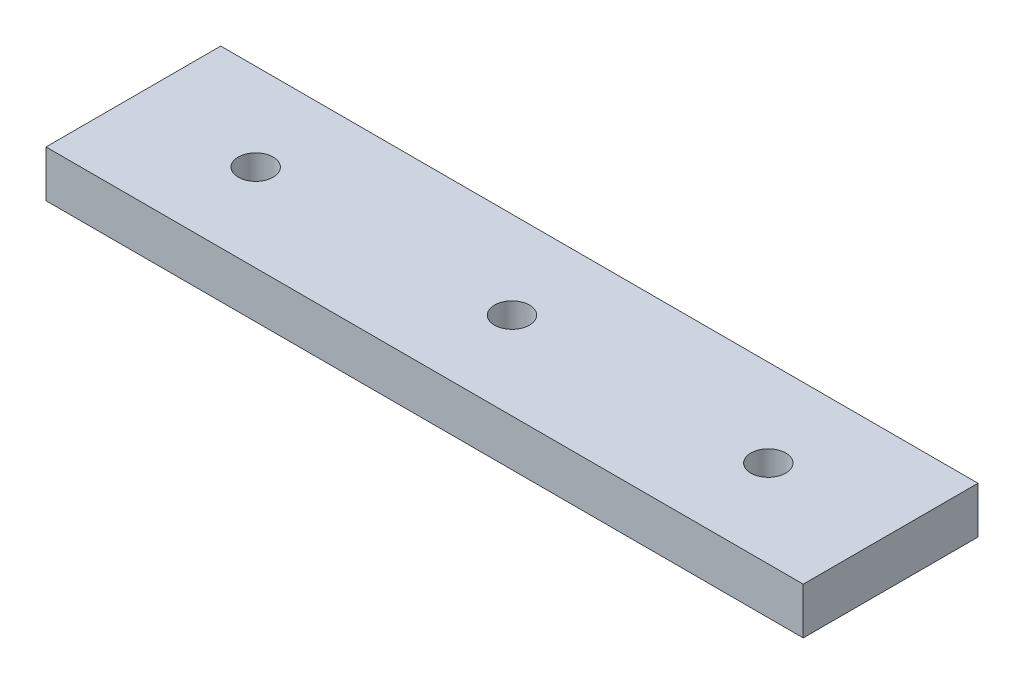
SolidWorks part; units mm, degrees
ref_plane "Alzado" through (0, 0, 0) normal (0, 0, 1) x (1, 0, 0)
ref_plane "Planta" through (0, 0, 0) normal (0, 1, 0) x (1, 0, 0)
ref_plane "Vista lateral" through (0, 0, 0) normal (1, 0, 0) x (0, 0, -1)
sketch "Croquis1" plane through (0, 0, 0) normal (0, 1, 0) x (1, 0, 0)
  line L1 (-32.5, -7.5) -> (32.5, -7.5)
  line L2 (-32.5, -7.5) -> (-32.5, 7.5)
  line L3 (-32.5, 7.5) -> (32.5, 7.5)
  line L4 (32.5, -7.5) -> (32.5, 7.5)
  line L5 (-32.5, -7.5) -> (32.5, 7.5) construction
  line L6 (-32.5, 7.5) -> (32.5, -7.5) construction
  point P0 (0, 0)
  dimension "D1" = 15
  dimension "D2" = 65
extrude "Saliente-Extruir1" add sketch "Croquis1" along normal blind 4
sketch "Croquis2" plane through (0, 4, 0) normal (0, 1, 0) x (1, 0, 0)
  line L0 (-22, 0) -> (0, 0) construction
  line L1 (0, 0) -> (22, 0) construction
  line L2 (-22, 0) -> (-32.5, 0) construction
  line L4 (-32.5, 7.5) -> (-32.5, -7.5) construction
  line L9 (32.5, -7.5) -> (32.5, 7.5) construction
  line L10 (32.5, 0) -> (22, 0) construction
  circle A0 centre (-22, 0) radius 1.5
  circle A1 centre (0, 0) radius 1.5
  circle A2 centre (22, 0) radius 1.5
  dimension "D1" = 3
  dimension "D2" = 22
extrude "Cortar-Extruir1" cut sketch "Croquis2" against normal through all
